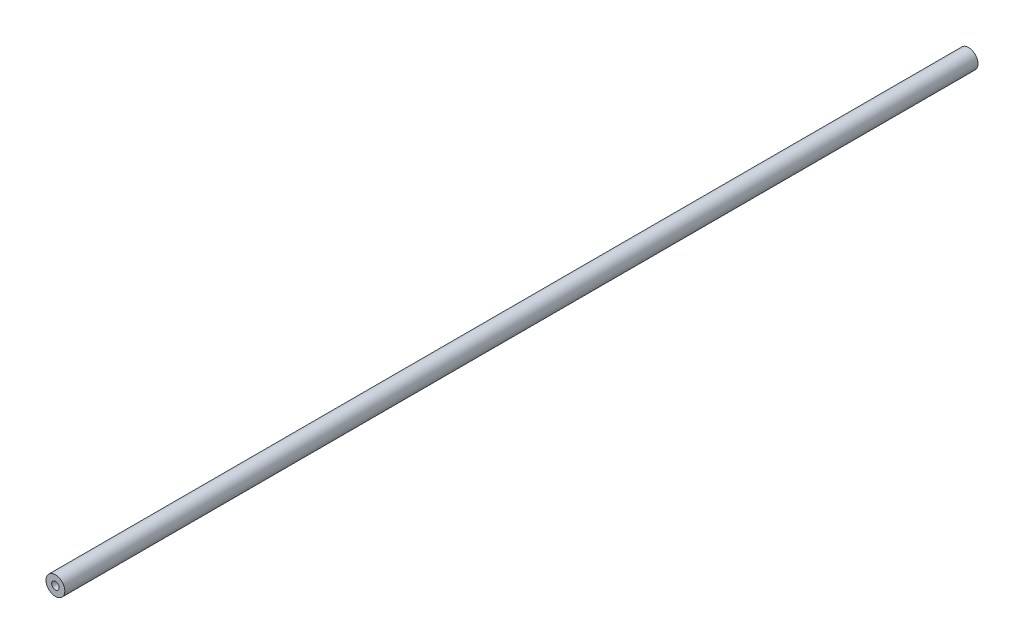
SolidWorks part; units mm, degrees
ref_plane "Front Plane" through (0, 0, 0) normal (0, 0, 1) x (1, 0, 0)
ref_plane "Top Plane" through (0, 0, 0) normal (0, 1, 0) x (1, 0, 0)
ref_plane "Right Plane" through (0, 0, 0) normal (1, 0, 0) x (0, 0, -1)
sketch "Sketch1" plane through (0, 0, 0) normal (0, 0, 1) x (1, 0, 0)
  circle A0 centre (0, 0) radius 3.175
  dimension "D1" = 6.35
extrude "Extrude1" add sketch "Sketch1" along normal blind 307.975
sketch "Sketch2" plane through (0, 0, 307.975) normal (0, 0, 1) x (1, 0, 0)
  circle A0 centre (0, 0) radius 1.27
  dimension "D1" = 2.54
extrude "Cut-Extrude1" cut sketch "Sketch2" against normal through all
